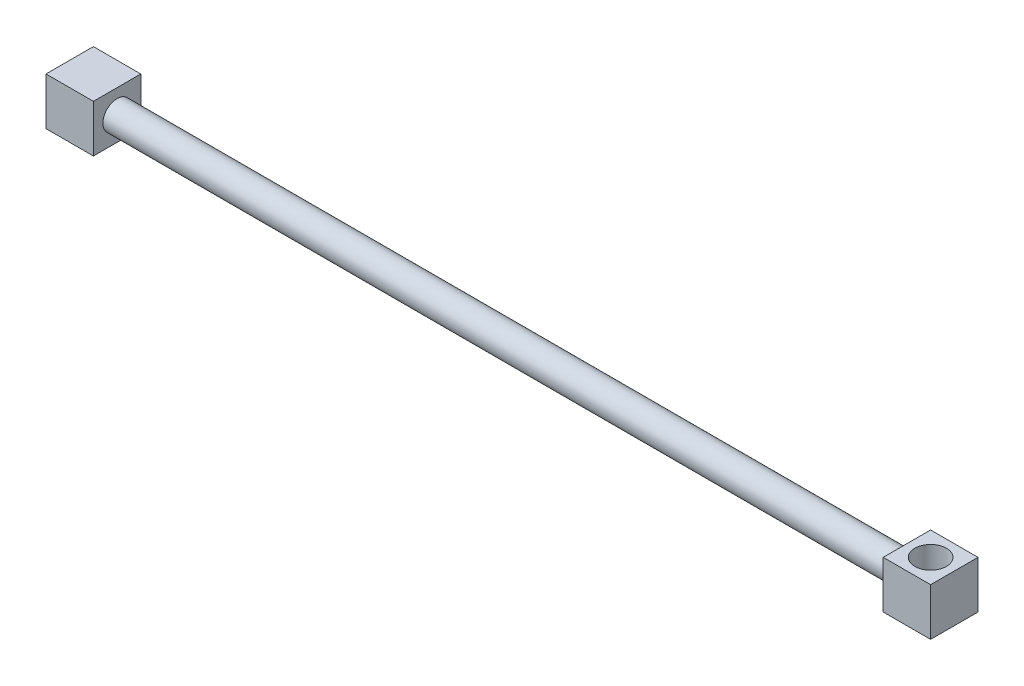
SolidWorks part; units mm, degrees
ref_plane "Front Plane" through (0, 0, 0) normal (0, 0, 1) x (1, 0, 0)
ref_plane "Top Plane" through (0, 0, 0) normal (0, 1, 0) x (1, 0, 0)
ref_plane "Right Plane" through (0, 0, 0) normal (1, 0, 0) x (0, 0, -1)
sketch "Sketch1" plane through (0, 0, 0) normal (1, 0, 0) x (0, 0, -1)
  line L1 (-15, 15) -> (15, 15)
  line L2 (-15, 15) -> (-15, -15)
  line L3 (-15, -15) -> (15, -15)
  line L4 (15, 15) -> (15, -15)
  line L5 (-15, 15) -> (15, -15) construction
  line L6 (-15, -15) -> (15, 15) construction
  point P0 (0, 0)
  dimension "D1" = 30
  dimension "D2" = 30
extrude "Boss-Extrude1" add sketch "Sketch1" along normal blind 30
sketch "Sketch2" plane through (30, 0, 0) normal (1, 0, 0) x (0, 0, -1)
  circle A0 centre (0, 0) radius 9
  dimension "D1" = 18
extrude "Boss-Extrude2" add sketch "Sketch2" along normal blind 500
sketch "Sketch3" plane through (530, 0, 0) normal (1, 0, 0) x (0, 0, -1)
  line L1 (-15, -15) -> (15, -15)
  line L2 (-15, -15) -> (-15, 15)
  line L3 (-15, 15) -> (15, 15)
  line L4 (15, -15) -> (15, 15)
  line L5 (-15, -15) -> (15, 15) construction
  line L6 (-15, 15) -> (15, -15) construction
  point P0 (0, 0)
  dimension "D1" = 30
  dimension "D2" = 30
extrude "Boss-Extrude3" add sketch "Sketch3" along normal blind 30
sketch "Sketch4" plane through (0, 15, 0) normal (0, 1, 0) x (1, 0, 0)
  line L0 (530, 15) -> (530, -15) construction
  line L2 (560, 15) -> (530, 15) construction
  circle A0 centre (545, 0) radius 10
  dimension "D1" = 20
  dimension "D2" = 15
  dimension "D3" = 15
extrude "Cut-Extrude1" cut sketch "Sketch4" against normal up to surface (30 mm away) up to face at (545, -15, 0)
